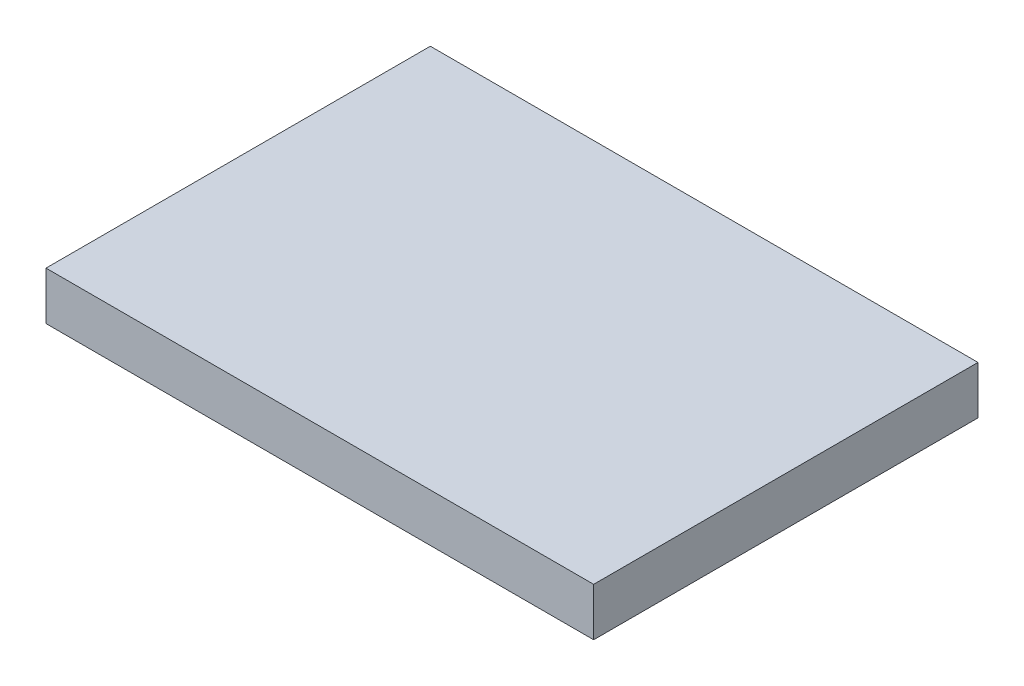
SolidWorks part; units mm, degrees
ref_plane "Alzado" through (0, 0, 0) normal (0, 0, 1) x (1, 0, 0)
ref_plane "Planta" through (0, 0, 0) normal (0, 1, 0) x (1, 0, 0)
ref_plane "Vista lateral" through (0, 0, 0) normal (1, 0, 0) x (0, 0, -1)
sketch "Croquis1" plane through (0, 0, 0) normal (0, 1, 0) x (1, 0, 0)
  line L1 (-40.8626, 12.4885) -> (16.1374, 12.4885)
  line L2 (-40.8626, 12.4885) -> (-40.8626, -27.5115)
  line L3 (-40.8626, -27.5115) -> (16.1374, -27.5115)
  line L4 (16.1374, 12.4885) -> (16.1374, -27.5115)
  dimension "D1" = 40
  dimension "D2" = 57
extrude "Saliente-Extruir1" add sketch "Croquis1" along normal blind 5
